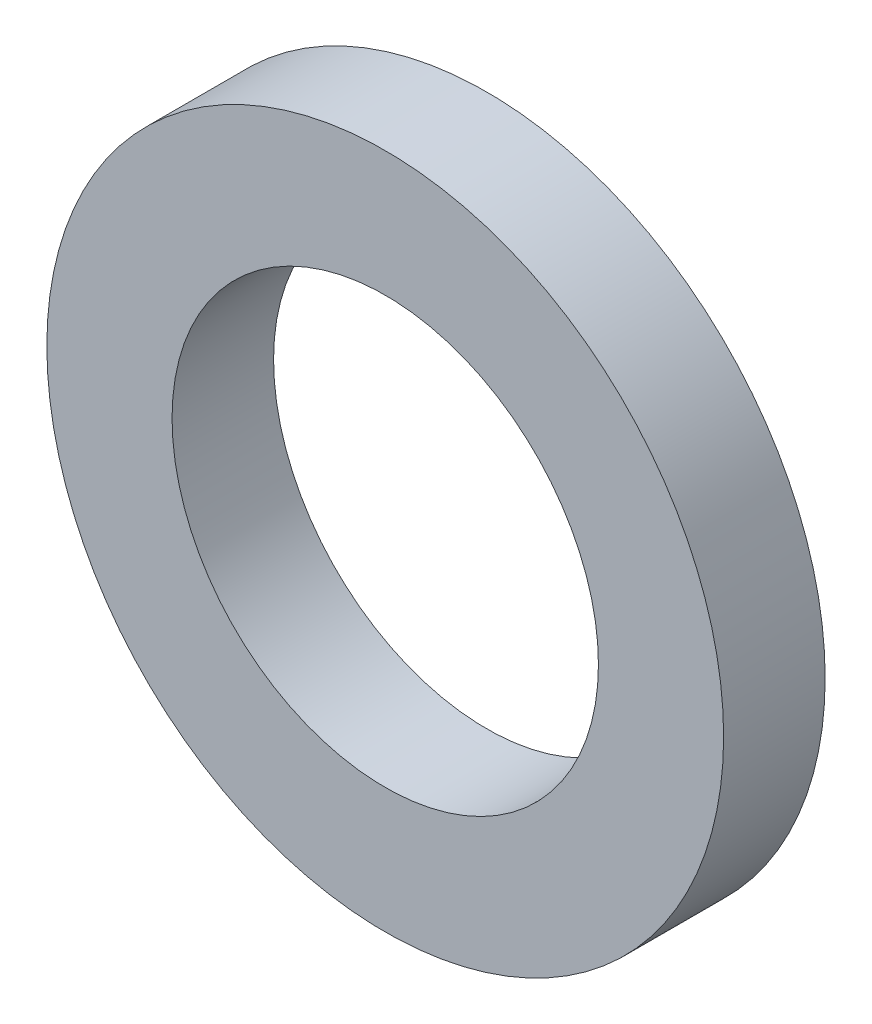
SolidWorks part; units mm, degrees
ref_plane "Front Plane" through (0, 0, 0) normal (0, 0, 1) x (1, 0, 0)
ref_plane "Top Plane" through (0, 0, 0) normal (0, 1, 0) x (1, 0, 0)
ref_plane "Right Plane" through (0, 0, 0) normal (1, 0, 0) x (0, 0, -1)
sketch "Sketch1" plane through (0, 0, 0) normal (0, 0, 1) x (1, 0, 0)
  circle A0 centre (0, 0) radius 10
  circle A1 centre (0, 0) radius 6.3
  dimension "D1" = 20
  dimension "D2" = 12.6
extrude "Boss-Extrude1" add sketch "Sketch1" along normal blind 3
